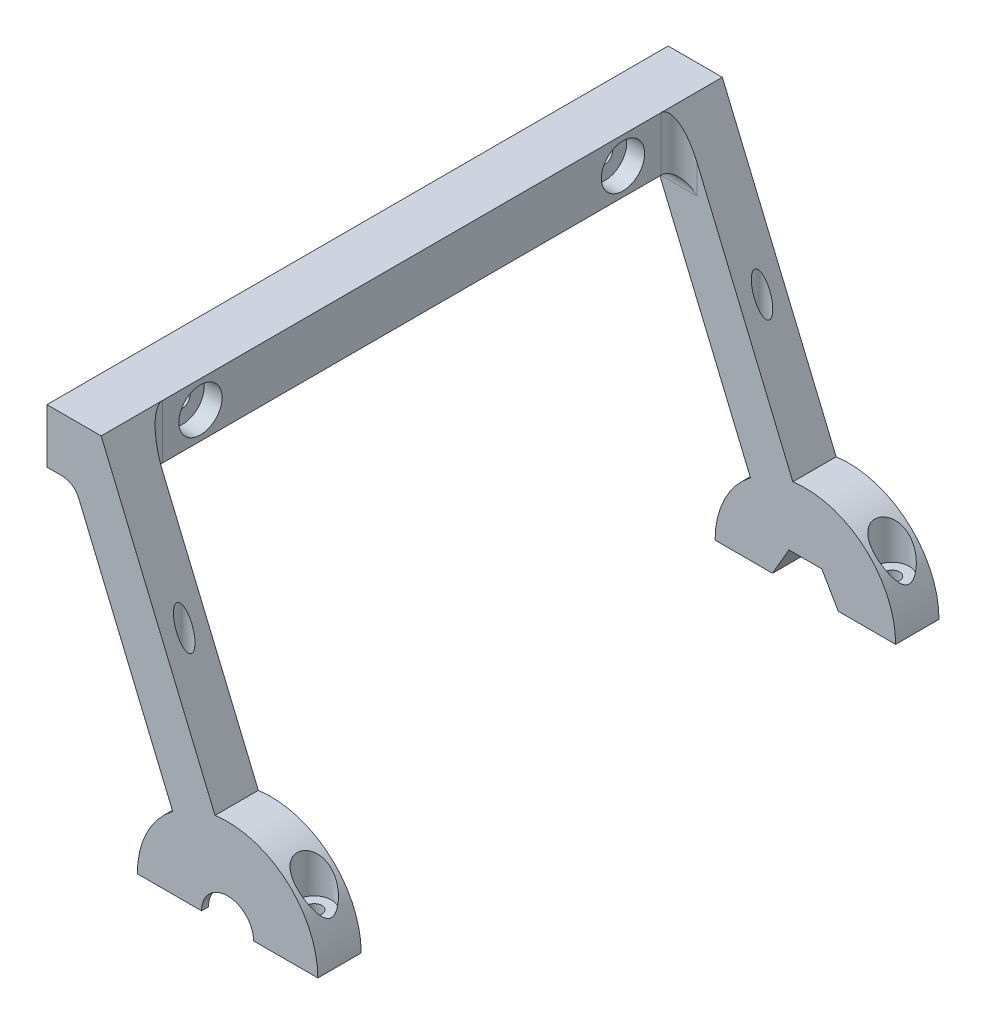
SolidWorks part; units mm, degrees
ref_plane "Front Plane" through (0, 0, 0) normal (0, 0, 1) x (1, 0, 0)
ref_plane "Top Plane" through (0, 0, 0) normal (0, 1, 0) x (1, 0, 0)
ref_plane "Right Plane" through (0, 0, 0) normal (1, 0, 0) x (0, 0, -1)
sketch "Sketch1" plane through (0, 0, 0) normal (0, 0, 1) x (1, 0, 0)
  line L1 (-7.5, -7.5) -> (7.5, -7.5)
  line L2 (-7.5, -7.5) -> (-7.5, 7.5)
  line L3 (-7.5, 7.5) -> (7.5, 7.5)
  line L4 (7.5, -7.5) -> (7.5, 7.5)
  line L5 (-7.5, -7.5) -> (7.5, 7.5) construction
  line L6 (-7.5, 7.5) -> (7.5, -7.5) construction
  point P0 (0, 0)
  dimension "D1" = 15
  dimension "D2" = 15
extrude "Boss-Extrude1" add sketch "Sketch1" along normal blind 86
sketch "Sketch2" plane through (0, 0, 86) normal (0, 0, 1) x (1, 0, 0)
  line L0 (7.5, 7.5) -> (49.3919, -92.5)
  line L1 (49.3919, -92.5) -> (35.6081, -92.5)
  line L2 (0, -7.5) -> (7.5, 7.5)
  line L3 (7.5, -7.5) -> (7.5, -92.5) construction
  line L4 (7.5, -92.5) -> (42.5, -92.5) construction
  line L5 (0, -7.5) -> (35.6081, -92.5)
  line L6 (-7.5, -7.5) -> (7.5, -7.5) construction
  dimension "D1" = 85
  dimension "D2" = 35
extrude "Boss-Extrude2" add sketch "Sketch2" against normal blind 12
sketch "Sketch3" plane through (7.5, 0, 0) normal (1, 0, 0) x (0, 0, -1)
  line L0 (0, -7.5) -> (0, 7.5) construction
  circle A0 centre (-58.5, 0) radius 6
  dimension "D1" = 12
  dimension "D2" = 58.5
extrude "Cut-Extrude1" cut sketch "Sketch3" against normal blind 5
sketch "Sketch4" plane through (2.5, 0, 0) normal (1, 0, 0) x (0, 0, -1)
  circle A0 centre (-58.5, 0) radius 2.1
  dimension "D1" = 4.2
extrude "Cut-Extrude2" cut sketch "Sketch4" against normal through all
sketch "Sketch5" plane through (0, 0, 86) normal (0, 0, 1) x (1, 0, 0)
  line L0 (35.6081, -92.5) -> (49.3919, -92.5) construction
  line L1 (17.5, -92.5) -> (67.5, -92.5)
  arc A0 (67.5, -92.5) -> (17.5, -92.5) centre (42.5, -92.5) ccw
  dimension "D1" = 50
extrude "Boss-Extrude5" add sketch "Sketch5" along direction (0, 0, 1) on the side against the normal up to surface (12 mm away) contours A0 L1
sketch "Sketch6" plane through (0, -92.5, 0) normal (0, -1, 0) x (1, 0, 0)
  line L0 (67.5, 80) -> (17.5, 80) construction
  line L1 (67.5, 74) -> (67.5, 86) construction
  line L2 (17.5, 74) -> (17.5, 86) construction
  line L3 (42.5, 80) -> (42.5, 19.048) construction
  circle A0 centre (24.5, 80) radius 2.1
  circle A1 centre (60.5, 80) radius 2.1
  dimension "D1" = 18
ref_plane "Plane1" through (0, -72.6555, 0) normal (0, 1, 0) x (1, 0, 0)
sketch "Sketch8" plane through (0, -72.6555, 0) normal (0, 1, 0) x (1, 0, 0)
  circle A0 centre (24.5, -80) radius 4.75
  circle A1 centre (60.5, -80) radius 4.75
  dimension "D1" = 9.5
  dimension "D2" = 9.5
extrude "Cut-Extrude4" cut sketch "Sketch8" against normal blind 10 and the other way blind 4
extrude "Cut-Extrude5" cut sketch "Sketch6" against normal through all
fillet "Fillet1" radius 5 3 edges at (0, -7.5, 80) (3.75, -7.5, 74) (7.5, 0, 74)
mirror "Mirror2" about plane through (0, 0, 0) normal (0, 0, -1) of bodies 108
sketch "Sketch9" plane through (0, 0, 86) normal (0, 0, 1) x (1, 0, 0)
  line L0 (17.5, -92.5) -> (67.5, -92.5) construction
  circle A0 centre (42.5, -92.5) radius 7.2
  dimension "D1" = 14.4
extrude "Cut-Extrude6" cut sketch "Sketch9" against normal up to next
sketch "Sketch10" plane through (0, 0, 86) normal (0, 0, 1) x (1, 0, 0)
  line L0 (17.5, -92.5) -> (67.5, -92.5) construction
  circle A0 centre (42.5, -92.5) radius 13.1
  dimension "D1" = 26.2
extrude "Cut-Extrude7" cut sketch "Sketch10" against normal blind 8.15 from offset 1.925 offset against normal yes
sketch "Sketch11" plane through (0, 0, -86) normal (0, 0, -1) x (-1, 0, 0)
  line L0 (-17.5, -92.5) -> (-67.5, -92.5) construction
  line L1 (-33.4, -92.5) -> (-37.95, -84.6192)
  line L2 (-37.95, -84.6192) -> (-47.05, -84.6192)
  line L3 (-47.05, -84.6192) -> (-51.6, -92.5)
  line L4 (-51.6, -92.5) -> (-47.05, -100.3808)
  line L5 (-47.05, -100.3808) -> (-37.95, -100.3808)
  line L6 (-37.95, -100.3808) -> (-33.4, -92.5)
  circle A0 centre (-42.5, -92.5) radius 7.8808 construction
  dimension "D1" = 18.2
extrude "Cut-Extrude8" cut sketch "Sketch11" against normal up to surface (12 mm away)
sketch "Sketch12" plane through (0, 0, 86) normal (0, 0, 1) x (1, 0, 0)
  circle A0 centre (42.5, -92.5) radius 50 construction
  dimension "D1" = 100
